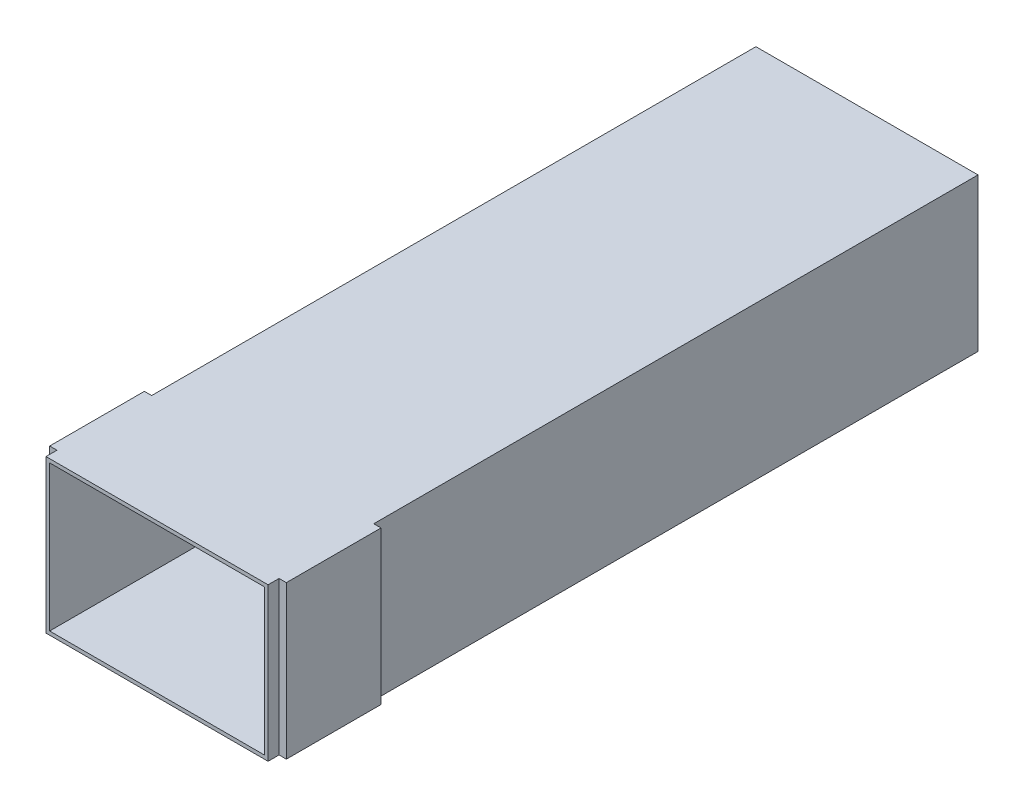
SolidWorks part; units mm, degrees
ref_plane "Front" through (0, 0, 0) normal (0, 0, 1) x (1, 0, 0)
ref_plane "Top" through (0, 0, 0) normal (0, 1, 0) x (1, 0, 0)
ref_plane "Right" through (0, 0, 0) normal (1, 0, 0) x (0, 0, -1)
sketch "Sketch1" plane through (0, 0, 0) normal (0, 1, 0) x (1, 0, 0)
  line L1 (-15.25, 7.9953) -> (0, 7.9953)
  line L2 (-15.25, 7.9953) -> (-15.25, -40.7547)
  line L3 (-15.25, -40.7547) -> (0, -40.7547)
  line L4 (0, 7.9953) -> (0, -40.7547)
extrude "Boss-Extrude1" add sketch "Sketch1" along normal blind 10.5
shell "Shell1" thickness 0.25
sketch "Sketch2" [suppressed] plane through (0, 9.75, 0) normal (0, 1, 0) x (1, 0, 0)
  line L0 (-16.5164, -40.7547) -> (-1.5164, -40.7547) construction
  line L1 (-9.6664, -40.7547) -> (-8.3664, -40.7547)
  line L2 (-9.6664, -40.7547) -> (-9.6664, -34.9547)
  line L3 (-9.6664, -34.9547) -> (-8.3664, -34.9547)
  line L4 (-8.3664, -40.7547) -> (-8.3664, -34.9547)
  line L5 (-16.5164, -39.0296) -> (-9.6664, -39.0296) construction
  line L6 (-16.5164, 7.9953) -> (-16.5164, -40.7547) construction
  line L7 (-5.9164, -40.7547) -> (-4.6164, -40.7547)
  line L8 (-8.3664, -39.0296) -> (-1.5164, -39.0296) construction
  line L9 (-1.5164, -40.7547) -> (-1.5164, 7.9953) construction
  line L10 (-5.9164, -40.7547) -> (-5.9164, -34.9547)
  line L11 (-5.9164, -34.9547) -> (-4.6164, -34.9547)
  line L12 (-4.6164, -40.7547) -> (-4.6164, -34.9547)
  line L14 (-9.6664, -40.7547) -> (-8.3664, -40.7547)
  line L15 (-9.6664, -40.7547) -> (-9.6664, -34.9547)
  line L16 (-9.6664, -34.9547) -> (-8.3664, -34.9547)
  line L17 (-8.3664, -40.7547) -> (-8.3664, -34.9547)
  line L18 (-16.5164, -39.0296) -> (-9.6664, -39.0296) construction
  line L19 (-13.4164, -40.7547) -> (-12.1164, -40.7547)
  line L20 (-13.4164, -40.7547) -> (-13.4164, -34.9547)
  line L21 (-13.4164, -34.9547) -> (-12.1164, -34.9547)
  line L22 (-12.1164, -40.7547) -> (-12.1164, -34.9547)
  line L24 (-20.2664, -39.0296) -> (-13.4164, -39.0296) construction
  line L25 (-12.7664, -39.0296) -> (-5.9164, -39.0296) construction
  dimension "D1" = 2
  dimension "D2" = 2
ref_plane "Plane1" through (-7.625, 0, 0) normal (-1, 0, 0) x (0, 0, 1)
sketch "Sketch3" plane through (0, 0, 0) normal (1, 0, 0) x (0, 0, -1)
  line L0 (-40.7547, 0) -> (7.9953, 0) construction
  line L1 (-40, 0) -> (-33.5, 0)
  line L2 (-40, 0) -> (-40, 10.5)
  line L3 (-40, 10.5) -> (-33.5, 10.5)
  line L4 (-33.5, 0) -> (-33.5, 10.5)
  line L5 (-40.7547, 10.5) -> (7.9953, 10.5) construction
extrude "Boss-Extrude2" add sketch "Sketch3" along normal blind 0.5
mirror "Mirror1" about plane through (-7.625, 0, 0) normal (-1, 0, 0) of "Boss-Extrude2"
